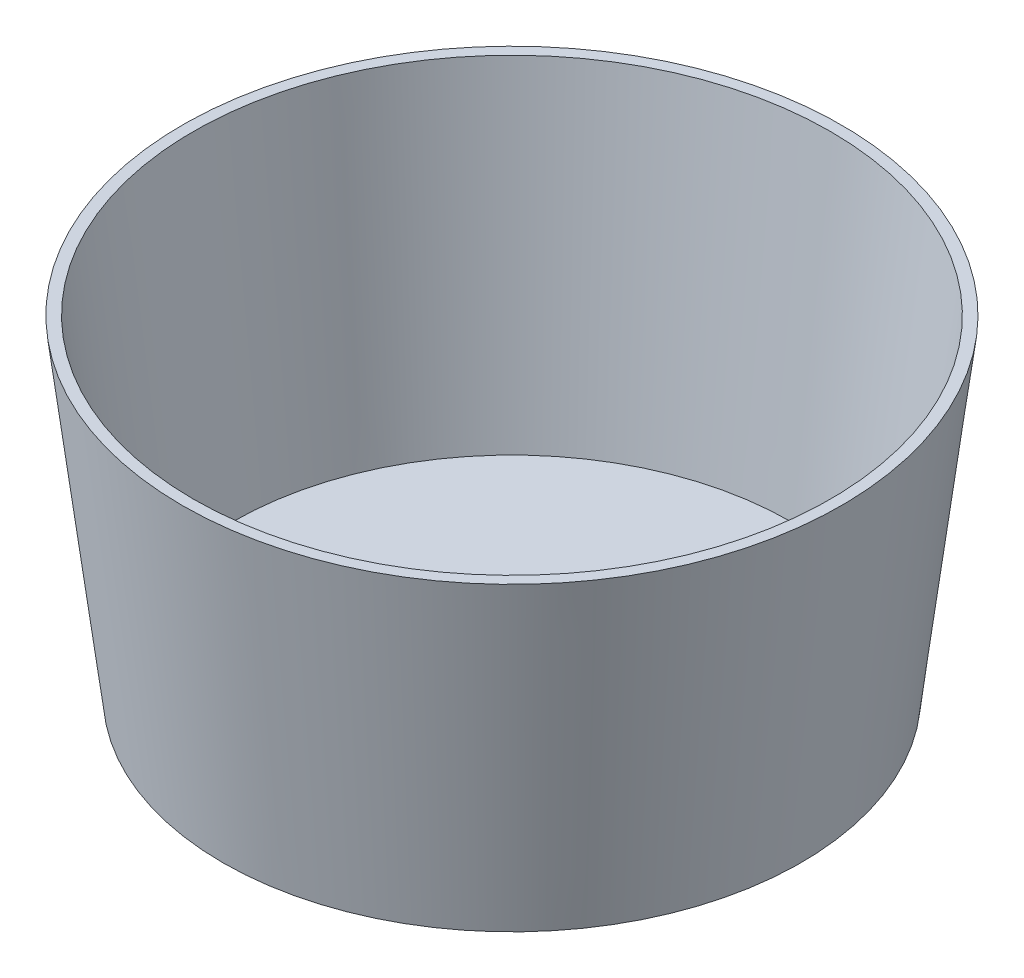
SolidWorks part; units mm, degrees
material "AISI 1020"
ref_plane "Front Plane" through (0, 0, 0) normal (0, 0, 1) x (1, 0, 0)
ref_plane "Top Plane" through (0, 0, 0) normal (0, 1, 0) x (1, 0, 0)
ref_plane "Right Plane" through (0, 0, 0) normal (1, 0, 0) x (0, 0, -1)
sketch "Sketch1" plane through (0, 0, 0) normal (0, 1, 0) x (1, 0, 0)
  circle A0 centre (0, 0) radius 300
  dimension "D1" = 600
extrude "Boss-Extrude1" add sketch "Sketch1" against normal blind 300 draft 7
shell "Shell2" thickness 10
